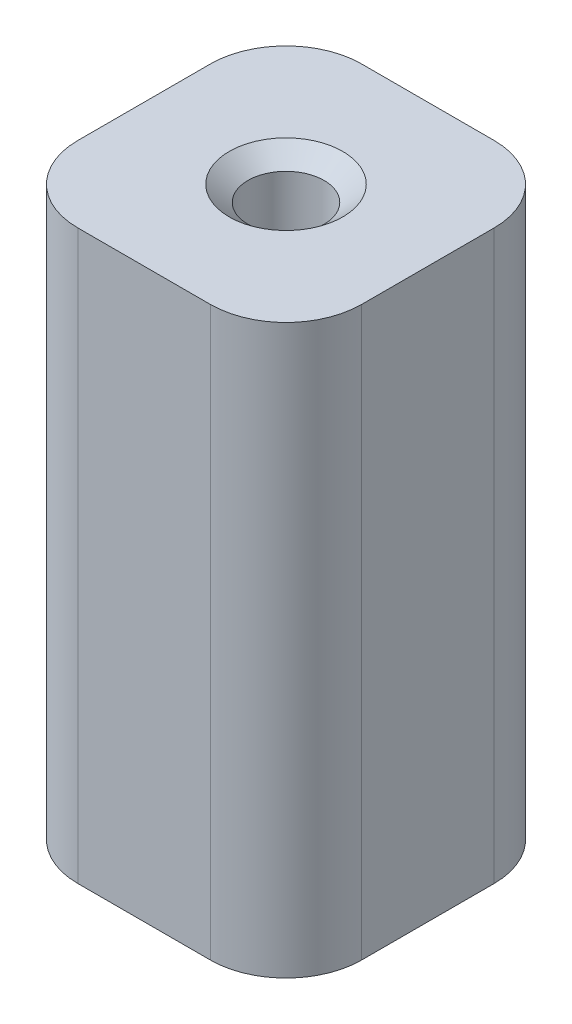
SolidWorks part; units mm, degrees
material "AISI 304"
ref_plane "Front Plane" through (0, 0, 0) normal (0, 0, 1) x (1, 0, 0)
ref_plane "Top Plane" through (0, 0, 0) normal (0, 1, 0) x (1, 0, 0)
ref_plane "Right Plane" through (0, 0, 0) normal (1, 0, 0) x (0, 0, -1)
sketch "Sketch1" plane through (0, 0, 0) normal (0, 1, 0) x (1, 0, 0)
  line L1 (-9.525, -9.525) -> (9.525, -9.525)
  line L2 (-9.525, -9.525) -> (-9.525, 9.525)
  line L3 (-9.525, 9.525) -> (9.525, 9.525)
  line L4 (9.525, -9.525) -> (9.525, 9.525)
  line L5 (-9.525, -9.525) -> (9.525, 9.525) construction
  line L6 (-9.525, 9.525) -> (9.525, -9.525) construction
  point P0 (0, 0)
  dimension "D1" = 19.05
extrude "Boss-Extrude1" add sketch "Sketch1" along normal blind 38.1
hole_wizard "1/4-20 Tapped Hole1" positions "Sketch4" profile "Sketch5" tap size "1/4-20" standard "ANSI Inch"
sketch "Sketch4" plane through (0, 38.1, 0) normal (0, 1, 0) x (1, 0, 0)
  point P0 (0, 0)
sketch "Sketch5" plane through (0, 38.1, 0) normal (1, 0, 0) x (0, 0, 1)
  line L0 (0, 0) -> (0, 26.9338)
  line L1 (0, 26.9338) -> (2.5527, 25.4)
  line L2 (2.5527, 25.4) -> (2.5527, 1.055)
  line L3 (2.5527, 1.055) -> (3.81, 0)
  line L5 (3.81, 0) -> (0, 0)
  line L6 (-2.5527, 1.055) -> (-3.81, 0) construction
  line L10 (0, 26.9338) -> (-2.5527, 25.4) construction
  line L11 (0, -6.35) -> (0, 107.95) construction
  dimension "Tap Drill Dia." = 5.1054
  dimension "Tap Drill Depth" = 25.4
  dimension "Near C'Sink Dia." = 7.62
  dimension "Near C'Sink Angle" = 100
  dimension "Drill Angle" = 118
cosmetic thread "Hole Thread2"
fillet "Fillet1" radius 5.08 4 edges at (-9.525, 19.05, 9.525) (-9.525, 19.05, -9.525) (9.525, 19.05, -9.525) (9.525, 19.05, 9.525)
